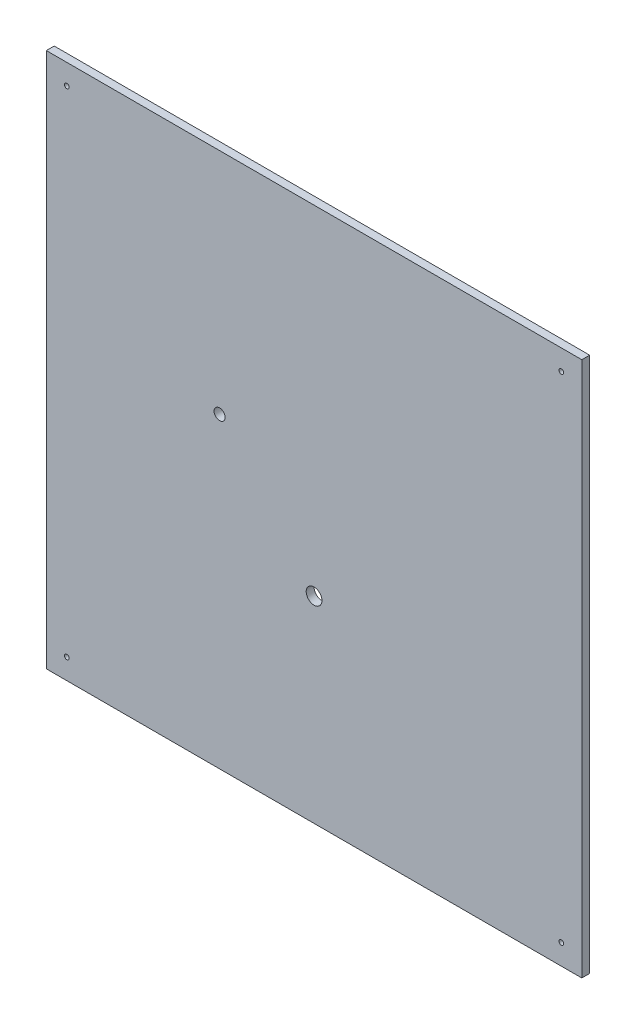
SolidWorks part; units mm, degrees
material "ABS"
ref_plane "Alzado" through (0, 0, 0) normal (0, 0, 1) x (1, 0, 0)
ref_plane "Planta" through (0, 0, 0) normal (0, 1, 0) x (1, 0, 0)
ref_plane "Vista lateral" through (0, 0, 0) normal (1, 0, 0) x (0, 0, -1)
sketch "Croquis1" plane through (0, 0, 0) normal (0, 0, 1) x (1, 0, 0)
  line L1 (-61.0528, 49.536) -> (278.9472, 49.536)
  line L2 (-61.0528, 49.536) -> (-61.0528, -290.464)
  line L3 (-61.0528, -290.464) -> (278.9472, -290.464)
  line L4 (278.9472, 49.536) -> (278.9472, -290.464)
  circle A0 centre (-48.0528, -277.464) radius 1.5
  circle A1 centre (-48.0528, 36.536) radius 1.5
  circle A2 centre (265.9472, -277.464) radius 1.5
  circle A3 centre (265.9472, 36.536) radius 1.5
  circle A4 centre (108.9472, -165.464) radius 5
  circle A5 centre (48.9472, -95.464) radius 3.5
  point P14 (108.9472, -290.464)
  dimension "D3" = 13
  dimension "D11" = 125
  dimension "D13" = 70
  dimension "D1" = 340
  dimension "D2" = 340
  dimension "D4" = 13
  dimension "D5" = 13
  dimension "D6" = 13
  dimension "D7" = 13
  dimension "D8" = 13
  dimension "D9" = 13
  dimension "D10" = 13
  dimension "D12" = 170
  dimension "D14" = 60
extrude "Saliente-Extruir1" add sketch "Croquis1" along normal blind 5
